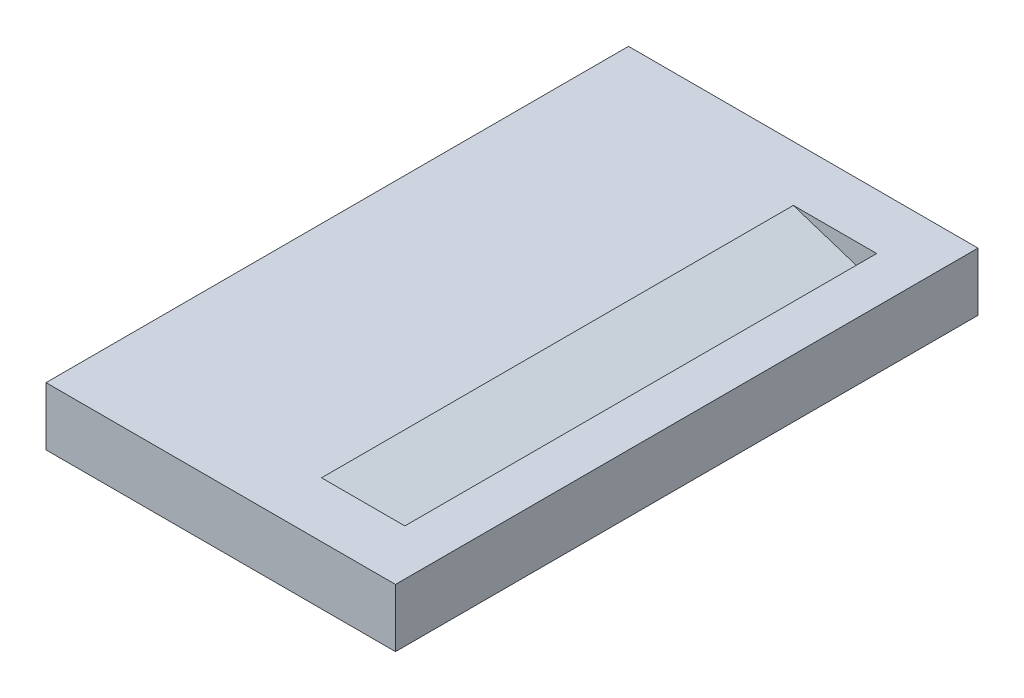
SolidWorks part; units mm, degrees
material "PE 高密度"
ref_plane "前基準面" through (0, 0, 0) normal (0, 0, 1) x (1, 0, 0)
ref_plane "上基準面" through (0, 0, 0) normal (0, 1, 0) x (1, 0, 0)
ref_plane "右基準面" through (0, 0, 0) normal (1, 0, 0) x (0, 0, -1)
sketch "草圖1" plane through (0, 0, 0) normal (0, 1, 0) x (1, 0, 0)
  line L1 (-44.775, -25) -> (44.775, -25)
  line L2 (-44.775, -25) -> (-44.775, 25)
  line L3 (-44.775, 25) -> (44.775, 25)
  line L4 (44.775, -25) -> (44.775, 25)
  line L5 (-44.775, -25) -> (44.775, 25) construction
  line L6 (-44.775, 25) -> (44.775, -25) construction
  point P0 (0, 0)
  dimension "D1" = 89.55
  dimension "D2" = 50
extrude "填料-伸長1" add sketch "草圖1" along normal blind 5
sketch "草圖2" plane through (0, 5, 0) normal (0, 1, 0) x (1, 0, 0)
  line L0 (-44.775, 25) -> (-44.775, -25) construction
  line L1 (-39.775, 5.2) -> (-7.375, 5.2)
  line L2 (-39.775, 5.2) -> (-39.775, 4)
  line L3 (-39.775, -5.2) -> (-7.375, -5.2)
  line L4 (-7.375, 5.2) -> (-7.375, -5.2)
  line L5 (-39.775, 5.2) -> (-7.375, -5.2) construction
  line L6 (-39.775, -5.2) -> (-7.375, 5.2) construction
  line L7 (-39.775, -4) -> (-39.775, -5.2)
  line L8 (-44.775, -4) -> (-39.775, -4)
  line L9 (-44.775, -4) -> (-44.775, 4)
  line L10 (-44.775, 4) -> (-39.775, 4)
  point P0 (-23.575, 0)
  point P12 (-44.775, 0)
  point P13 (-7.375, 0)
  dimension "D1" = 5
  dimension "D2" = 32.4
  dimension "D3" = 10.4
  dimension "D4" = 8
extrude "除料-伸長1" cut sketch "草圖2" against normal blind 4
sketch "草圖4" plane through (0, 0, 0) normal (0, 0, 1) x (1, 0, 0)
  line L0 (-27.155, 5) -> (-27.155, 32)
  line L1 (-44.775, 5) -> (44.775, 5) construction
  line L2 (-27.155, 32) -> (55.9425, 5)
  line L3 (-39.775, 1) -> (-39.775, 5) construction
  dimension "D1" = 18
  dimension "D2" = 27
  dimension "D3" = 12.62
ref_plane "平面1" through (5.7451, 17.6816, 0) normal (0.309, 0.9511, 0) x (0, 0, -1)
sketch "草圖6" plane through (5.7451, 17.6816, 0) normal (0.309, 0.9511, 0) x (0, 0, -1)
  line L1 (-20.25, -37.2855) -> (20.25, -37.2855)
  line L2 (-20.25, -37.2855) -> (-20.25, 55.7145)
  line L3 (-20.25, 55.7145) -> (20.25, 55.7145)
  line L4 (20.25, -37.2855) -> (20.25, 55.7145)
  point P4 (0, -37.2855)
  dimension "D1" = 40.5
  dimension "D2" = 20
  dimension "D3" = 93
extrude "除料-伸長2" cut sketch "草圖6" against normal blind 3.43
sketch "草圖7" plane through (0, 0, 25) normal (0, 0, 1) x (1, 0, 0)
  line L0 (-44.775, 5) -> (44.775, 5) construction
  line L1 (-44.775, 0) -> (14.775, 0)
  line L2 (-44.775, 0) -> (-44.775, 5)
  line L3 (-44.775, 5) -> (14.775, 5)
  line L4 (14.775, 0) -> (14.775, 5)
  line L5 (44.775, 5) -> (44.775, 0) construction
  dimension "D1" = 30
extrude "除料-伸長3" cut sketch "草圖7" against normal through all
